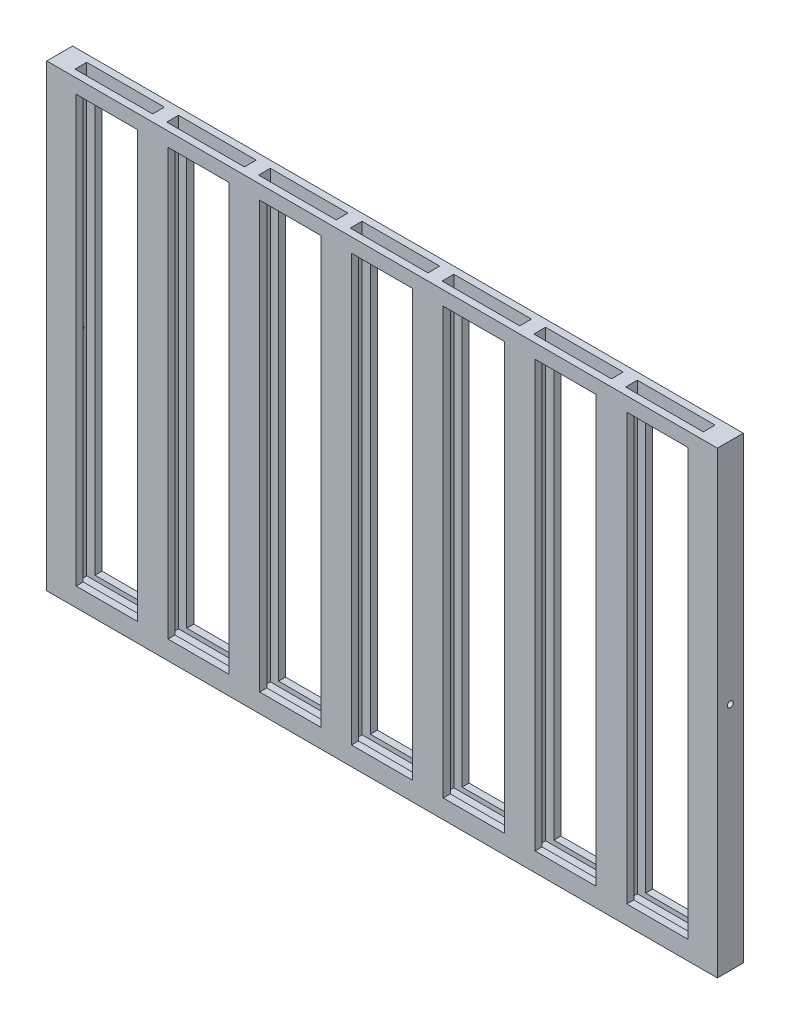
SolidWorks part; units mm, degrees
ref_plane "Front Plane" through (0, 0, 0) normal (0, 0, 1) x (1, 0, 0)
ref_plane "Top Plane" through (0, 0, 0) normal (0, 1, 0) x (1, 0, 0)
ref_plane "Right Plane" through (0, 0, 0) normal (1, 0, 0) x (0, 0, -1)
sketch "Sketch2" plane through (0, 0, 0) normal (0, 0, 1) x (1, 0, 0)
  line L1 (-285, -195) -> (285, -195)
  line L2 (-285, -195) -> (-285, 195)
  line L3 (-285, 195) -> (285, 195)
  line L4 (285, -195) -> (285, 195)
  line L5 (-285, -195) -> (285, 195) construction
  line L6 (-285, 195) -> (285, -195) construction
  point P0 (0, 0)
  dimension "D1" = 390
  dimension "D2" = 570
extrude "Boss-Extrude1" add sketch "Sketch2" along normal blind 22
sketch "Sketch4" plane through (0, 195, 0) normal (0, 1, 0) x (1, 0, 0)
  line L1 (267, -6) -> (-267, -6)
  line L2 (267, -6) -> (267, -16)
  line L3 (267, -16) -> (-267, -16)
  line L4 (-267, -6) -> (-267, -16)
  line L5 (267, -6) -> (-267, -16) construction
  line L6 (267, -16) -> (-267, -6) construction
  point P0 (0, -11)
  dimension "D1" = 10
  dimension "D2" = 534
extrude "Cut-Extrude1" cut sketch "Sketch4" against normal blind 378
sketch "Sketch5" plane through (0, 195, 0) normal (0, 1, 0) x (1, 0, 0)
  line L0 (-267, -16) -> (267, -16) construction
  line L1 (201, -16) -> (189, -16)
  line L2 (201, -16) -> (201, -6)
  line L3 (201, -6) -> (189, -6)
  line L4 (189, -16) -> (189, -6)
  line L5 (267, -6) -> (-267, -6) construction
  line L7 (267, -16) -> (267, -6) construction
  line L8 (123, -16) -> (123, -6)
  line L9 (123, -16) -> (111, -16)
  line L10 (111, -16) -> (111, -6)
  line L11 (123, -6) -> (111, -6)
  line L12 (45, -16) -> (45, -6)
  line L13 (45, -16) -> (33, -16)
  line L14 (33, -16) -> (33, -6)
  line L15 (45, -6) -> (33, -6)
  line L16 (-33, -16) -> (-33, -6)
  line L17 (-33, -16) -> (-45, -16)
  line L18 (-45, -16) -> (-45, -6)
  line L19 (-33, -6) -> (-45, -6)
  line L20 (-111, -16) -> (-111, -6)
  line L21 (-111, -16) -> (-123, -16)
  line L22 (-123, -16) -> (-123, -6)
  line L23 (-111, -6) -> (-123, -6)
  line L24 (-189, -16) -> (-189, -6)
  line L25 (-189, -16) -> (-201, -16)
  line L26 (-201, -16) -> (-201, -6)
  line L27 (-189, -6) -> (-201, -6)
  dimension "D1" = 12
  dimension "D2" = 66
  dimension "D3" = 6
extrude "Boss-Extrude2" add sketch "Sketch5" against normal blind 378
sketch "Sketch3" plane through (0, 0, 0) normal (0, 0, -1) x (-1, 0, 0)
  line L3 (-182, 183) -> (-182, -179)
  line L4 (-260, 183) -> (-208, 183)
  line L5 (-260, 183) -> (-260, -179)
  line L7 (-260, -179) -> (-208, -179)
  line L8 (-208, 183) -> (-208, -179)
  line L9 (-182, 183) -> (-130, 183)
  line L10 (-130, 183) -> (-130, -179)
  line L11 (-182, -179) -> (-130, -179)
  line L12 (-104, 183) -> (-104, -179)
  line L13 (-104, 183) -> (-52, 183)
  line L14 (-52, 183) -> (-52, -179)
  line L15 (-104, -179) -> (-52, -179)
  line L16 (-26, 183) -> (-26, -179)
  line L17 (-26, 183) -> (26, 183)
  line L18 (26, 183) -> (26, -179)
  line L19 (-26, -179) -> (26, -179)
  line L20 (52, 183) -> (52, -179)
  line L21 (52, 183) -> (104, 183)
  line L22 (104, 183) -> (104, -179)
  line L23 (52, -179) -> (104, -179)
  line L24 (130, 183) -> (130, -179)
  line L25 (130, 183) -> (182, 183)
  line L26 (182, 183) -> (182, -179)
  line L27 (130, -179) -> (182, -179)
  line L28 (208, 183) -> (208, -179)
  line L29 (208, 183) -> (260, 183)
  line L30 (260, 183) -> (260, -179)
  line L31 (208, -179) -> (260, -179)
  line L32 (285, -195) -> (-285, -195) construction
  dimension "D1" = 7
  dimension "D2" = 16
sketch "Sketch6" plane through (-285, 0, 0) normal (-1, 0, 0) x (0, 0, 1)
  line L0 (11, 195) -> (11, -195) construction
  line L1 (22, 195) -> (0, 195) construction
  line L2 (22, -195) -> (0, -195) construction
  circle A0 centre (11, 1) radius 2.5
  dimension "D1" = 5
  dimension "D2" = 194
extrude "Cut-Extrude3" cut sketch "Sketch6" against normal up to next
sketch "Sketch7" plane through (285, 0, 0) normal (1, 0, 0) x (0, 0, -1)
  line L0 (-11, 195) -> (-11, -195) construction
  line L1 (-22, 195) -> (0, 195) construction
  line L2 (-22, -195) -> (0, -195) construction
  circle A0 centre (-11, 1) radius 2.5
  dimension "D1" = 5
  dimension "D2" = 194
extrude "Cut-Extrude4" cut sketch "Sketch7" against normal up to next
extrude "Cut-Extrude5" cut sketch "Sketch3" against normal through all
